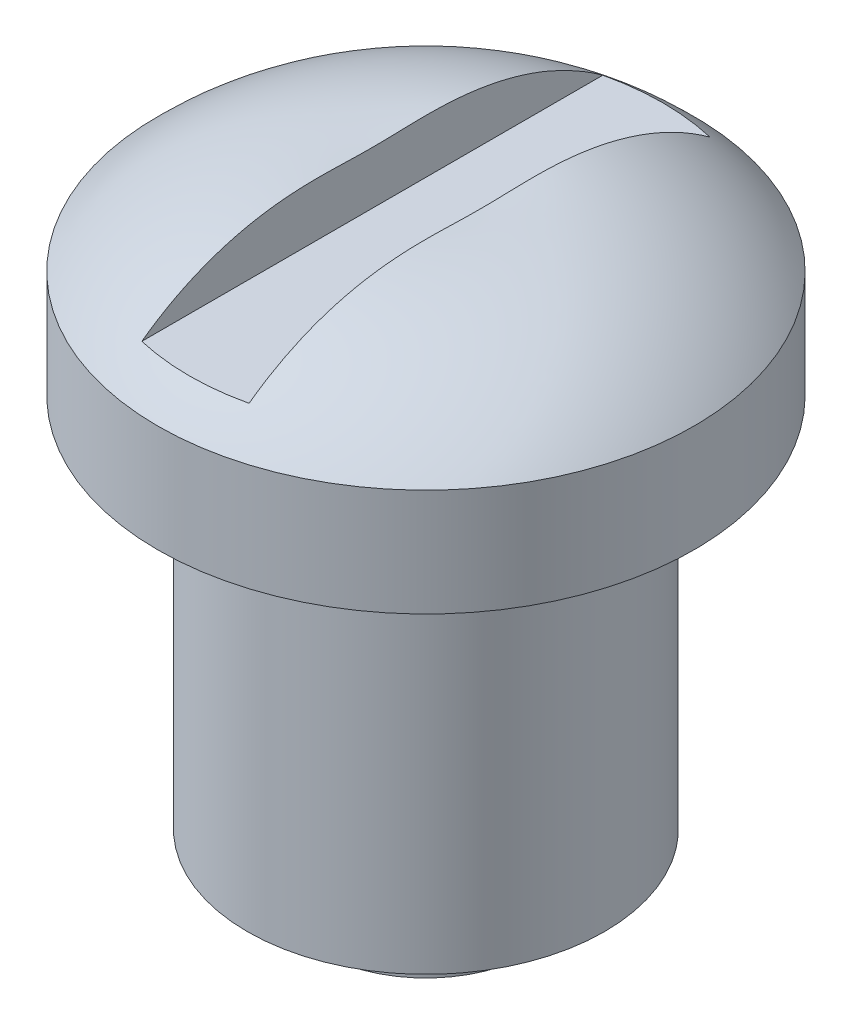
SolidWorks part; units mm, degrees
ref_plane "Front Plane" through (0, 0, 0) normal (0, 0, 1) x (1, 0, 0)
ref_plane "Top Plane" through (0, 0, 0) normal (0, 1, 0) x (1, 0, 0)
ref_plane "Right Plane" through (0, 0, 0) normal (1, 0, 0) x (0, 0, -1)
sketch "Sketch1" plane through (0, 0, 0) normal (0, 0, 1) x (1, 0, 0)
  line L0 (0, 5) -> (0, -5)
  line L1 (0, -5) -> (2, -5)
  line L2 (2, -5) -> (2, -4)
  line L3 (2, -4) -> (3.33, -4)
  line L4 (3.33, -4) -> (3.33, 3)
  line L5 (3.33, 3) -> (5, 3)
  line L6 (5, 3) -> (5, 5)
  line L8 (0, 5) -> (0, 5.5)
  line L9 (0, 5.5) -> (1, 5.5)
  line L10 (1, 5.5) -> (1, 6.5)
  arc A0 (1, 6.5) -> (5, 5) centre (1.4126, 1.5171) cw
  point P4 (0, 0)
  dimension "D1" = 5
  dimension "D2" = 2
  dimension "D3" = 1
  dimension "D4" = 7
  dimension "D5" = 1
  dimension "D6" = 0.5
revolve "Revolve1" add sketch "Sketch1" angle 360 about L0
sketch "Sketch2" plane through (0, 5.5, 0) normal (0, 1, 0) x (1, 0, 0)
  circle A0 centre (0, 0) radius 1
extrude "Boss-Extrude1" add sketch "Sketch2" along normal blind 1
sketch "Sketch3" plane through (0, 0, 0) normal (0, 0, 1) x (1, 0, 0)
  line L0 (-1, 6.5171) -> (1, 6.5171)
  line L1 (1.4126, 6.5171) -> (-1.4126, 6.5171) construction
  line L2 (-1, 6.5171) -> (-1, 5.5171)
  line L3 (-1, 5.5171) -> (1, 5.5171)
  line L4 (1, 5.5171) -> (1, 6.5171)
  point P5 (0, 6.5171)
extrude "Cut-Extrude1" cut sketch "Sketch3" against normal mid plane 10
